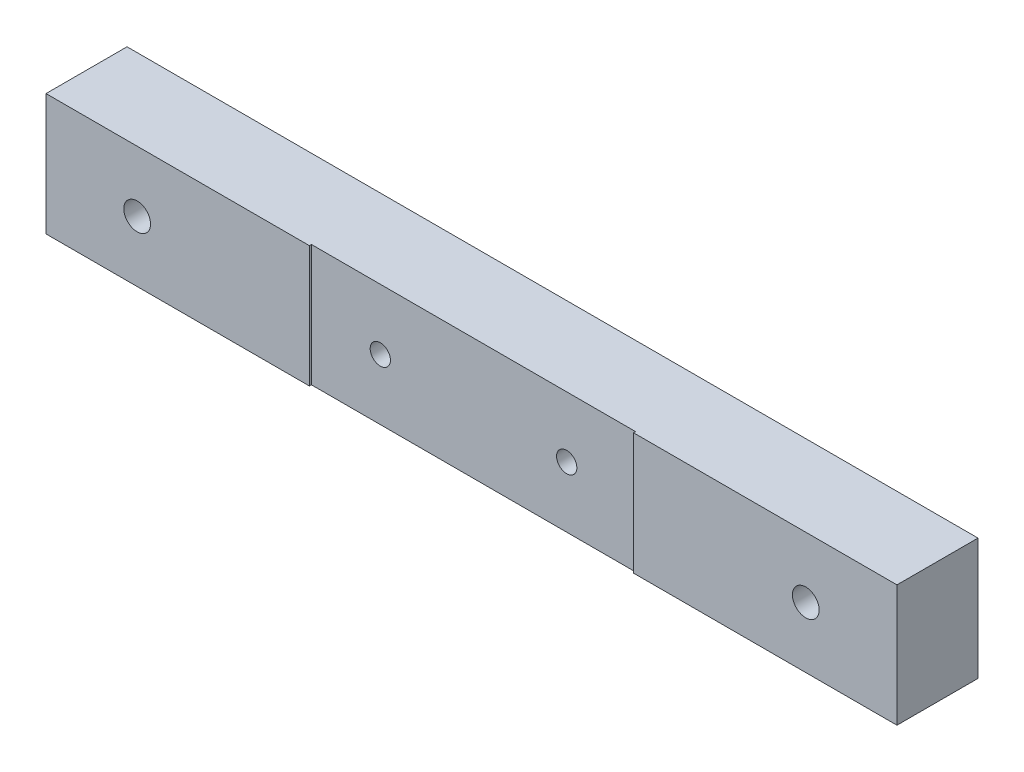
SolidWorks part; units mm, degrees
material "1023 Листовая углеродистая сталь (SS)"
ref_plane "Front" through (0, 0, 0) normal (0, 0, 1) x (1, 0, 0)
ref_plane "Top" through (0, 0, 0) normal (0, 1, 0) x (1, 0, 0)
ref_plane "Right" through (0, 0, 0) normal (1, 0, 0) x (0, 0, -1)
sketch "Sketch1" plane through (0, 0, 0) normal (0, 0, 1) x (1, 0, 0)
  line L1 (-105, 15) -> (105, 15)
  line L2 (-105, 15) -> (-105, -15)
  line L3 (-105, -15) -> (105, -15)
  line L4 (105, 15) -> (105, -15)
  line L5 (-105, 15) -> (105, -15) construction
  line L6 (-105, -15) -> (105, 15) construction
  point P0 (0, 0)
  dimension "D1" = 30
  dimension "D2" = 210
extrude "Extrude1" add sketch "Sketch1" along normal blind 20
hole_wizard "CBORE for M6 Hex Head Flange Bolt1" positions "Sketch2" profile "Sketch3" counterbore size "M6" standard "DIN" end condition through all
sketch "Sketch2" plane through (0, 0, 0) normal (0, 0, -1) x (-1, 0, 0)
  line L0 (82.5, 0) -> (-82.5, 0)
  point P0 (82.5, 0)
  point P2 (-82.5, 0)
  dimension "D1" = 165
sketch "Sketch3" plane through (-82.5, 0, 0) normal (1, 0, 0) x (0, 1, 0)
  line L0 (0, 0) -> (0, 20)
  line L1 (0, 20) -> (3.3, 20)
  line L3 (3.3, 20) -> (3.3, 6.6)
  line L4 (3.3, 6.6) -> (8, 6.6)
  line L5 (8, 6.6) -> (8, 0)
  line L7 (8, 0) -> (0, 0)
  line L11 (0, -6.35) -> (0, 107.95) construction
  dimension "Диаметр сквозного отверстия" = 6.6
  dimension "Глубина сквозного отверстия" = 20
  dimension "Диаметр цековки" = 16
  dimension "Глубина цековки" = 6.6
sketch "Sketch4" plane through (0, 15, 0) normal (0, 1, 0) x (1, 0, 0)
  line L0 (105, -20) -> (-105, -20) construction
  line L1 (-40, -19.5) -> (40, -19.5)
  line L2 (-40, -19.5) -> (-40, -20)
  line L3 (-40, -20) -> (40, -20)
  line L4 (40, -19.5) -> (40, -20)
  line L5 (0, 0) -> (0, -19.5) construction
  dimension "D1" = 0.5
  dimension "D2" = 80
extrude "Cut-Extrude1" cut sketch "Sketch4" against normal up to next
hole_wizard "M6 Tapped Hole1" positions "Sketch5" profile "Sketch6" tap size "M6" standard "DIN" end condition through all
sketch "Sketch5" plane through (0, 0, 19.5) normal (0, 0, 1) x (1, 0, 0)
  point P0 (-23, 0)
  point P3 (23, 0)
sketch "Sketch6" plane through (-23, 0, 19.5) normal (1, 0, 0) x (0, -1, 0)
  line L0 (0, 0) -> (0, 19.5)
  line L1 (0, 19.5) -> (2.5, 19.5)
  line L2 (2.5, 19.5) -> (2.5, 0)
  line L5 (2.5, 0) -> (0, 0)
  line L11 (0, -6.35) -> (0, 107.95) construction
  dimension "Диаметр проходного сверла" = 5
  dimension "Глубина проходного сверла" = 19.5
cosmetic thread "Cosmetic Thread1" parameters "D2"=6
cosmetic thread "Cosmetic Thread2" parameters "D2"=6
